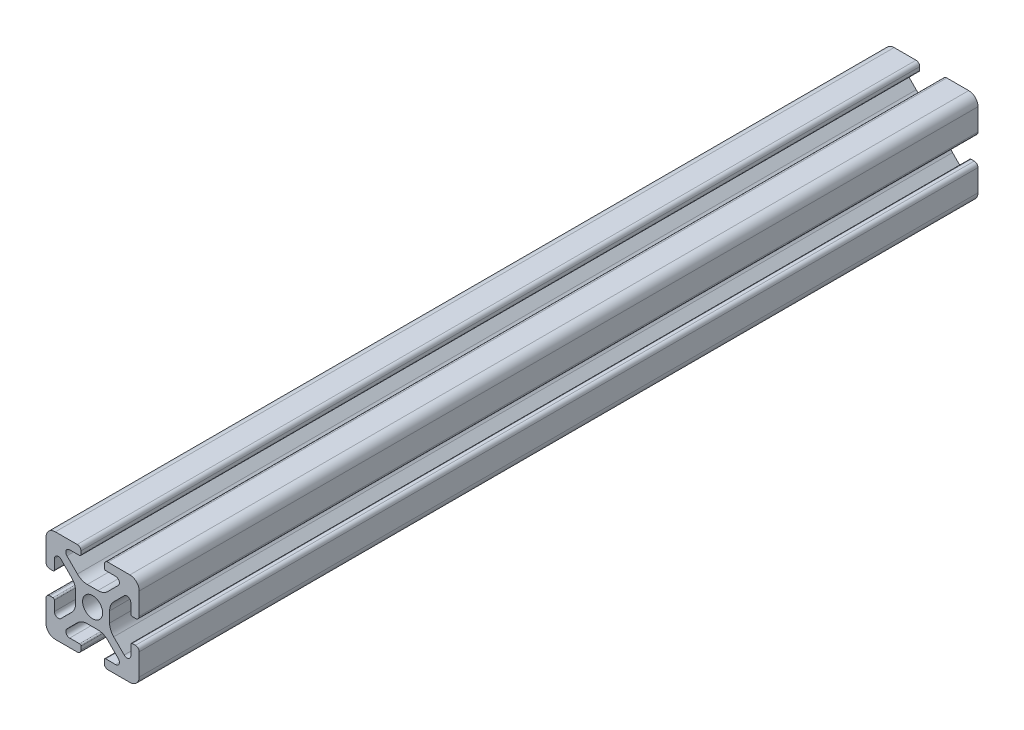
SolidWorks part; units mm, degrees
ref_plane "Front" through (0, 0, 0) normal (0, 0, 1) x (1, 0, 0)
ref_plane "Top" through (0, 0, 0) normal (0, 1, 0) x (1, 0, 0)
ref_plane "Right" through (0, 0, 0) normal (1, 0, 0) x (0, 0, -1)
sketch "Support-Front" plane through (0, 0, 0) normal (0, 0, 1) x (1, 0, 0)
  line L0 (10, 0) -> (-10, 0) construction
  line L1 (-10, -10) -> (10, -10)
  line L2 (-10, -10) -> (-10, 10)
  line L3 (-10, 10) -> (10, 10)
  line L4 (10, -10) -> (10, 10)
  line L5 (0, 10) -> (0, -10) construction
  dimension "Height-Profile" = 20
  dimension "Width-Profile" = 20
sketch "Support-Right-Length" plane through (0, 0, 0) normal (1, 0, 0) x (0, 0, -1)
  line L0 (0, -10) -> (0, 10) construction
  line L1 (-25, 10) -> (25, 10)
  line L2 (-25, 10) -> (-25, -10)
  line L3 (-25, -10) -> (25, -10)
  line L4 (25, 10) -> (25, -10)
  dimension "Length-Profile" = 50
sketch "Support-Profile" plane through (0, 0, 0) normal (0, 0, 1) x (1, 0, 0)
  line L8 (4.9176, -8.2) -> (2.8, -8.2)
  line L9 (2.5, -8.5) -> (2.5, -9.2)
  line L10 (3.3, -10) -> (8, -10)
  line L11 (10, -8) -> (10, -3.3)
  line L24 (9.2, -2.5) -> (8.5, -2.5)
  line L25 (8.2, -2.8) -> (8.2, -4.9176)
  line L26 (6.779, -5.5062) -> (4.5287, -3.2559)
  line L27 (3.65, -1.1346) -> (3.65, 1.1346)
  line L28 (4.5287, 3.2559) -> (6.779, 5.5062)
  line L29 (8.2, 4.9176) -> (8.2, 2.8)
  line L30 (8.5, 2.5) -> (9.2, 2.5)
  line L31 (10, 3.3) -> (10, 8)
  line L32 (8, 10) -> (3.3, 10)
  line L33 (2.5, 9.2) -> (2.5, 8.5)
  line L34 (2.8, 8.2) -> (4.9176, 8.2)
  line L35 (5.5062, 6.779) -> (3.2559, 4.5287)
  line L40 (1.1346, 3.65) -> (-1.1346, 3.65)
  line L41 (-3.2559, 4.5287) -> (-5.5062, 6.779)
  line L42 (-4.9176, 8.2) -> (-2.8, 8.2)
  line L43 (-2.5, 8.5) -> (-2.5, 9.2)
  line L44 (-3.3, 10) -> (-8, 10)
  line L45 (-10, 8) -> (-10, 3.3)
  line L46 (-9.2, 2.5) -> (-8.5, 2.5)
  line L47 (-8.2, 2.8) -> (-8.2, 4.9176)
  line L48 (-6.779, 5.5062) -> (-4.5287, 3.2559)
  line L49 (-3.65, 1.1346) -> (-3.65, -1.1346)
  line L50 (-4.5287, -3.2559) -> (-6.779, -5.5062)
  line L51 (-8.2, -4.9176) -> (-8.2, -2.8)
  line L52 (-8.5, -2.5) -> (-9.2, -2.5)
  line L53 (-10, -3.3) -> (-10, -8)
  line L54 (-8, -10) -> (-3.3, -10)
  line L55 (-2.5, -9.2) -> (-2.5, -8.5)
  line L56 (-2.8, -8.2) -> (-4.9176, -8.2)
  line L57 (-5.5062, -6.779) -> (-3.2559, -4.5287)
  line L58 (-1.1346, -3.65) -> (1.1346, -3.65)
  line L59 (3.2559, -4.5287) -> (5.5062, -6.779)
  circle A2 centre (0, 0) radius 2.15
  arc A3 (2.8, -8.2) -> (2.5, -8.5) centre (2.8, -8.5) ccw
  arc A5 (2.5, -9.2) -> (3.3, -10) centre (3.3, -9.2) ccw
  arc A24 (8, -10) -> (10, -8) centre (8, -8) ccw
  arc A25 (10, -3.3) -> (9.2, -2.5) centre (9.2, -3.3) ccw
  arc A26 (8.5, -2.5) -> (8.2, -2.8) centre (8.5, -2.8) ccw
  arc A27 (6.779, -5.5062) -> (8.2, -4.9176) centre (7.3676, -4.9176) ccw
  arc A28 (3.65, -1.1346) -> (4.5287, -3.2559) centre (6.65, -1.1346) ccw
  arc A29 (4.5287, 3.2559) -> (3.65, 1.1346) centre (6.65, 1.1346) ccw
  arc A30 (8.2, 4.9176) -> (6.779, 5.5062) centre (7.3676, 4.9176) ccw
  arc A31 (8.2, 2.8) -> (8.5, 2.5) centre (8.5, 2.8) ccw
  arc A32 (9.2, 2.5) -> (10, 3.3) centre (9.2, 3.3) ccw
  arc A33 (10, 8) -> (8, 10) centre (8, 8) ccw
  arc A34 (3.3, 10) -> (2.5, 9.2) centre (3.3, 9.2) ccw
  arc A35 (2.5, 8.5) -> (2.8, 8.2) centre (2.8, 8.5) ccw
  arc A38 (5.5062, 6.779) -> (4.9176, 8.2) centre (4.9176, 7.3676) ccw
  arc A39 (1.1346, 3.65) -> (3.2559, 4.5287) centre (1.1346, 6.65) ccw
  arc A44 (-3.2559, 4.5287) -> (-1.1346, 3.65) centre (-1.1346, 6.65) ccw
  arc A45 (-4.9176, 8.2) -> (-5.5062, 6.779) centre (-4.9176, 7.3676) ccw
  arc A46 (-2.8, 8.2) -> (-2.5, 8.5) centre (-2.8, 8.5) ccw
  arc A47 (-2.5, 9.2) -> (-3.3, 10) centre (-3.3, 9.2) ccw
  arc A48 (-8, 10) -> (-10, 8) centre (-8, 8) ccw
  arc A49 (-10, 3.3) -> (-9.2, 2.5) centre (-9.2, 3.3) ccw
  arc A50 (-8.5, 2.5) -> (-8.2, 2.8) centre (-8.5, 2.8) ccw
  arc A51 (-6.779, 5.5062) -> (-8.2, 4.9176) centre (-7.3676, 4.9176) ccw
  arc A52 (-3.65, 1.1346) -> (-4.5287, 3.2559) centre (-6.65, 1.1346) ccw
  arc A53 (-4.5287, -3.2559) -> (-3.65, -1.1346) centre (-6.65, -1.1346) ccw
  arc A54 (-8.2, -4.9176) -> (-6.779, -5.5062) centre (-7.3676, -4.9176) ccw
  arc A55 (-8.2, -2.8) -> (-8.5, -2.5) centre (-8.5, -2.8) ccw
  arc A56 (-9.2, -2.5) -> (-10, -3.3) centre (-9.2, -3.3) ccw
  arc A57 (-10, -8) -> (-8, -10) centre (-8, -8) ccw
  arc A58 (-3.3, -10) -> (-2.5, -9.2) centre (-3.3, -9.2) ccw
  arc A59 (-2.5, -8.5) -> (-2.8, -8.2) centre (-2.8, -8.5) ccw
  arc A60 (-5.5062, -6.779) -> (-4.9176, -8.2) centre (-4.9176, -7.3676) ccw
  arc A61 (-1.1346, -3.65) -> (-3.2559, -4.5287) centre (-1.1346, -6.65) ccw
  arc A62 (3.2559, -4.5287) -> (1.1346, -3.65) centre (1.1346, -6.65) ccw
  arc A63 (4.9176, -8.2) -> (5.5062, -6.779) centre (4.9176, -7.3676) ccw
ref_plane "Ref-Plane-1" through (0, 0, 25) normal (0, 0, 1) x (1, 0, 0)
ref_plane "Ref-Plane-2" through (0, 0, -25) normal (0, 0, 1) x (1, 0, 0)
sketch "Sketch4" plane through (0, 0, 25) normal (0, 0, 1) x (1, 0, 0)
  line L0 (-10, -10) -> (-10, 10) construction
  line L1 (-10, -10) -> (10, -10) construction
  line L2 (10, -10) -> (10, 10) construction
  line L3 (-10, 10) -> (10, 10) construction
  line L4 (-10, -10) -> (-10, 10)
  line L5 (-10, -10) -> (10, -10)
  line L6 (10, -10) -> (10, 10)
  line L7 (-10, 10) -> (10, 10)
extrude "Body" add sketch "Sketch4" against normal blind 180
sketch "Sketch16" plane through (0, 0, 0) normal (0, 0, 1) x (1, 0, 0)
  line L40 (4.9176, -8.2) -> (2.8, -8.2)
  line L41 (2.5, -8.5) -> (2.5, -9.2)
  line L42 (3.3, -10) -> (8, -10)
  line L43 (10, -8) -> (10, -3.3)
  line L44 (9.2, -2.5) -> (8.5, -2.5)
  line L45 (8.2, -2.8) -> (8.2, -4.9176)
  line L46 (6.779, -5.5062) -> (4.5287, -3.2559)
  line L47 (3.65, -1.1346) -> (3.65, 1.1346)
  line L48 (4.5287, 3.2559) -> (6.779, 5.5062)
  line L49 (8.2, 4.9176) -> (8.2, 2.8)
  line L50 (8.5, 2.5) -> (9.2, 2.5)
  line L51 (10, 3.3) -> (10, 8)
  line L52 (8, 10) -> (3.3, 10)
  line L53 (2.5, 9.2) -> (2.5, 8.5)
  line L54 (2.8, 8.2) -> (4.9176, 8.2)
  line L55 (5.5062, 6.779) -> (3.2559, 4.5287)
  line L56 (1.1346, 3.65) -> (-1.1346, 3.65)
  line L57 (-3.2559, 4.5287) -> (-5.5062, 6.779)
  line L58 (-4.9176, 8.2) -> (-2.8, 8.2)
  line L59 (-2.5, 8.5) -> (-2.5, 9.2)
  line L60 (-3.3, 10) -> (-8, 10)
  line L61 (-10, 8) -> (-10, 3.3)
  line L62 (-9.2, 2.5) -> (-8.5, 2.5)
  line L63 (-8.2, 2.8) -> (-8.2, 4.9176)
  line L64 (-6.779, 5.5062) -> (-4.5287, 3.2559)
  line L65 (-3.65, 1.1346) -> (-3.65, -1.1346)
  line L66 (-4.5287, -3.2559) -> (-6.779, -5.5062)
  line L67 (-8.2, -4.9176) -> (-8.2, -2.8)
  line L68 (-8.5, -2.5) -> (-9.2, -2.5)
  line L69 (-10, -3.3) -> (-10, -8)
  line L70 (-8, -10) -> (-3.3, -10)
  line L71 (-2.5, -9.2) -> (-2.5, -8.5)
  line L72 (-2.8, -8.2) -> (-4.9176, -8.2)
  line L73 (-5.5062, -6.779) -> (-3.2559, -4.5287)
  line L74 (-1.1346, -3.65) -> (1.1346, -3.65)
  line L75 (3.2559, -4.5287) -> (5.5062, -6.779)
  line L76 (4.9176, -8.2) -> (2.8, -8.2)
  line L77 (2.5, -8.5) -> (2.5, -9.2)
  line L78 (3.3, -10) -> (8, -10)
  line L79 (10, -8) -> (10, -3.3)
  line L80 (9.2, -2.5) -> (8.5, -2.5)
  line L81 (8.2, -2.8) -> (8.2, -4.9176)
  line L82 (6.779, -5.5062) -> (4.5287, -3.2559)
  line L83 (3.65, -1.1346) -> (3.65, 1.1346)
  line L84 (4.5287, 3.2559) -> (6.779, 5.5062)
  line L85 (8.2, 4.9176) -> (8.2, 2.8)
  line L86 (8.5, 2.5) -> (9.2, 2.5)
  line L87 (10, 3.3) -> (10, 8)
  line L88 (8, 10) -> (3.3, 10)
  line L89 (2.5, 9.2) -> (2.5, 8.5)
  line L90 (2.8, 8.2) -> (4.9176, 8.2)
  line L91 (5.5062, 6.779) -> (3.2559, 4.5287)
  line L92 (1.1346, 3.65) -> (-1.1346, 3.65)
  line L93 (-3.2559, 4.5287) -> (-5.5062, 6.779)
  line L94 (-4.9176, 8.2) -> (-2.8, 8.2)
  line L95 (-2.5, 8.5) -> (-2.5, 9.2)
  line L96 (-3.3, 10) -> (-8, 10)
  line L97 (-10, 8) -> (-10, 3.3)
  line L98 (-9.2, 2.5) -> (-8.5, 2.5)
  line L99 (-8.2, 2.8) -> (-8.2, 4.9176)
  line L100 (-6.779, 5.5062) -> (-4.5287, 3.2559)
  line L101 (-3.65, 1.1346) -> (-3.65, -1.1346)
  line L102 (-4.5287, -3.2559) -> (-6.779, -5.5062)
  line L103 (-8.2, -4.9176) -> (-8.2, -2.8)
  line L104 (-8.5, -2.5) -> (-9.2, -2.5)
  line L105 (-10, -3.3) -> (-10, -8)
  line L106 (-8, -10) -> (-3.3, -10)
  line L107 (-2.5, -9.2) -> (-2.5, -8.5)
  line L108 (-2.8, -8.2) -> (-4.9176, -8.2)
  line L109 (-5.5062, -6.779) -> (-3.2559, -4.5287)
  line L110 (-1.1346, -3.65) -> (1.1346, -3.65)
  line L111 (3.2559, -4.5287) -> (5.5062, -6.779)
  circle A7 centre (0, 0) radius 2.15 construction
  circle A8 centre (0, 0) radius 2.15
  arc A43 (2.8, -8.2) -> (2.5, -8.5) centre (2.8, -8.5) ccw
  arc A44 (2.5, -9.2) -> (3.3, -10) centre (3.3, -9.2) ccw
  arc A45 (8, -10) -> (10, -8) centre (8, -8) ccw
  arc A46 (10, -3.3) -> (9.2, -2.5) centre (9.2, -3.3) ccw
  arc A47 (8.5, -2.5) -> (8.2, -2.8) centre (8.5, -2.8) ccw
  arc A48 (6.779, -5.5062) -> (8.2, -4.9176) centre (7.3676, -4.9176) ccw
  arc A49 (3.65, -1.1346) -> (4.5287, -3.2559) centre (6.65, -1.1346) ccw
  arc A50 (4.5287, 3.2559) -> (3.65, 1.1346) centre (6.65, 1.1346) ccw
  arc A51 (8.2, 4.9176) -> (6.779, 5.5062) centre (7.3676, 4.9176) ccw
  arc A52 (8.2, 2.8) -> (8.5, 2.5) centre (8.5, 2.8) ccw
  arc A53 (9.2, 2.5) -> (10, 3.3) centre (9.2, 3.3) ccw
  arc A54 (10, 8) -> (8, 10) centre (8, 8) ccw
  arc A55 (3.3, 10) -> (2.5, 9.2) centre (3.3, 9.2) ccw
  arc A56 (2.5, 8.5) -> (2.8, 8.2) centre (2.8, 8.5) ccw
  arc A57 (5.5062, 6.779) -> (4.9176, 8.2) centre (4.9176, 7.3676) ccw
  arc A58 (1.1346, 3.65) -> (3.2559, 4.5287) centre (1.1346, 6.65) ccw
  arc A59 (-3.2559, 4.5287) -> (-1.1346, 3.65) centre (-1.1346, 6.65) ccw
  arc A60 (-4.9176, 8.2) -> (-5.5062, 6.779) centre (-4.9176, 7.3676) ccw
  arc A61 (-2.8, 8.2) -> (-2.5, 8.5) centre (-2.8, 8.5) ccw
  arc A62 (-2.5, 9.2) -> (-3.3, 10) centre (-3.3, 9.2) ccw
  arc A63 (-8, 10) -> (-10, 8) centre (-8, 8) ccw
  arc A64 (-10, 3.3) -> (-9.2, 2.5) centre (-9.2, 3.3) ccw
  arc A65 (-8.5, 2.5) -> (-8.2, 2.8) centre (-8.5, 2.8) ccw
  arc A66 (-6.779, 5.5062) -> (-8.2, 4.9176) centre (-7.3676, 4.9176) ccw
  arc A67 (-3.65, 1.1346) -> (-4.5287, 3.2559) centre (-6.65, 1.1346) ccw
  arc A68 (-4.5287, -3.2559) -> (-3.65, -1.1346) centre (-6.65, -1.1346) ccw
  arc A69 (-8.2, -4.9176) -> (-6.779, -5.5062) centre (-7.3676, -4.9176) ccw
  arc A70 (-8.2, -2.8) -> (-8.5, -2.5) centre (-8.5, -2.8) ccw
  arc A71 (-9.2, -2.5) -> (-10, -3.3) centre (-9.2, -3.3) ccw
  arc A72 (-10, -8) -> (-8, -10) centre (-8, -8) ccw
  arc A73 (-3.3, -10) -> (-2.5, -9.2) centre (-3.3, -9.2) ccw
  arc A74 (-2.5, -8.5) -> (-2.8, -8.2) centre (-2.8, -8.5) ccw
  arc A75 (-5.5062, -6.779) -> (-4.9176, -8.2) centre (-4.9176, -7.3676) ccw
  arc A76 (-1.1346, -3.65) -> (-3.2559, -4.5287) centre (-1.1346, -6.65) ccw
  arc A77 (3.2559, -4.5287) -> (1.1346, -3.65) centre (1.1346, -6.65) ccw
  arc A78 (4.9176, -8.2) -> (5.5062, -6.779) centre (4.9176, -7.3676) ccw
  arc A79 (2.8, -8.2) -> (2.5, -8.5) centre (2.8, -8.5) ccw
  arc A80 (2.5, -9.2) -> (3.3, -10) centre (3.3, -9.2) ccw
  arc A81 (8, -10) -> (10, -8) centre (8, -8) ccw
  arc A82 (10, -3.3) -> (9.2, -2.5) centre (9.2, -3.3) ccw
  arc A83 (8.5, -2.5) -> (8.2, -2.8) centre (8.5, -2.8) ccw
  arc A84 (6.779, -5.5062) -> (8.2, -4.9176) centre (7.3676, -4.9176) ccw
  arc A85 (3.65, -1.1346) -> (4.5287, -3.2559) centre (6.65, -1.1346) ccw
  arc A86 (4.5287, 3.2559) -> (3.65, 1.1346) centre (6.65, 1.1346) ccw
  arc A87 (8.2, 4.9176) -> (6.779, 5.5062) centre (7.3676, 4.9176) ccw
  arc A88 (8.2, 2.8) -> (8.5, 2.5) centre (8.5, 2.8) ccw
  arc A89 (9.2, 2.5) -> (10, 3.3) centre (9.2, 3.3) ccw
  arc A90 (10, 8) -> (8, 10) centre (8, 8) ccw
  arc A91 (3.3, 10) -> (2.5, 9.2) centre (3.3, 9.2) ccw
  arc A92 (2.5, 8.5) -> (2.8, 8.2) centre (2.8, 8.5) ccw
  arc A93 (5.5062, 6.779) -> (4.9176, 8.2) centre (4.9176, 7.3676) ccw
  arc A94 (1.1346, 3.65) -> (3.2559, 4.5287) centre (1.1346, 6.65) ccw
  arc A95 (-3.2559, 4.5287) -> (-1.1346, 3.65) centre (-1.1346, 6.65) ccw
  arc A96 (-4.9176, 8.2) -> (-5.5062, 6.779) centre (-4.9176, 7.3676) ccw
  arc A97 (-2.8, 8.2) -> (-2.5, 8.5) centre (-2.8, 8.5) ccw
  arc A98 (-2.5, 9.2) -> (-3.3, 10) centre (-3.3, 9.2) ccw
  arc A99 (-8, 10) -> (-10, 8) centre (-8, 8) ccw
  arc A100 (-10, 3.3) -> (-9.2, 2.5) centre (-9.2, 3.3) ccw
  arc A101 (-8.5, 2.5) -> (-8.2, 2.8) centre (-8.5, 2.8) ccw
  arc A102 (-6.779, 5.5062) -> (-8.2, 4.9176) centre (-7.3676, 4.9176) ccw
  arc A103 (-3.65, 1.1346) -> (-4.5287, 3.2559) centre (-6.65, 1.1346) ccw
  arc A104 (-4.5287, -3.2559) -> (-3.65, -1.1346) centre (-6.65, -1.1346) ccw
  arc A105 (-8.2, -4.9176) -> (-6.779, -5.5062) centre (-7.3676, -4.9176) ccw
  arc A106 (-8.2, -2.8) -> (-8.5, -2.5) centre (-8.5, -2.8) ccw
  arc A107 (-9.2, -2.5) -> (-10, -3.3) centre (-9.2, -3.3) ccw
  arc A108 (-10, -8) -> (-8, -10) centre (-8, -8) ccw
  arc A109 (-3.3, -10) -> (-2.5, -9.2) centre (-3.3, -9.2) ccw
  arc A110 (-2.5, -8.5) -> (-2.8, -8.2) centre (-2.8, -8.5) ccw
  arc A111 (-5.5062, -6.779) -> (-4.9176, -8.2) centre (-4.9176, -7.3676) ccw
  arc A112 (-1.1346, -3.65) -> (-3.2559, -4.5287) centre (-1.1346, -6.65) ccw
  arc A113 (3.2559, -4.5287) -> (1.1346, -3.65) centre (1.1346, -6.65) ccw
  arc A114 (4.9176, -8.2) -> (5.5062, -6.779) centre (4.9176, -7.3676) ccw
  dimension "D1" = 0
extrude "Cut-Profile" cut sketch "Sketch16" against normal through all and the other way through all flip side to cut
